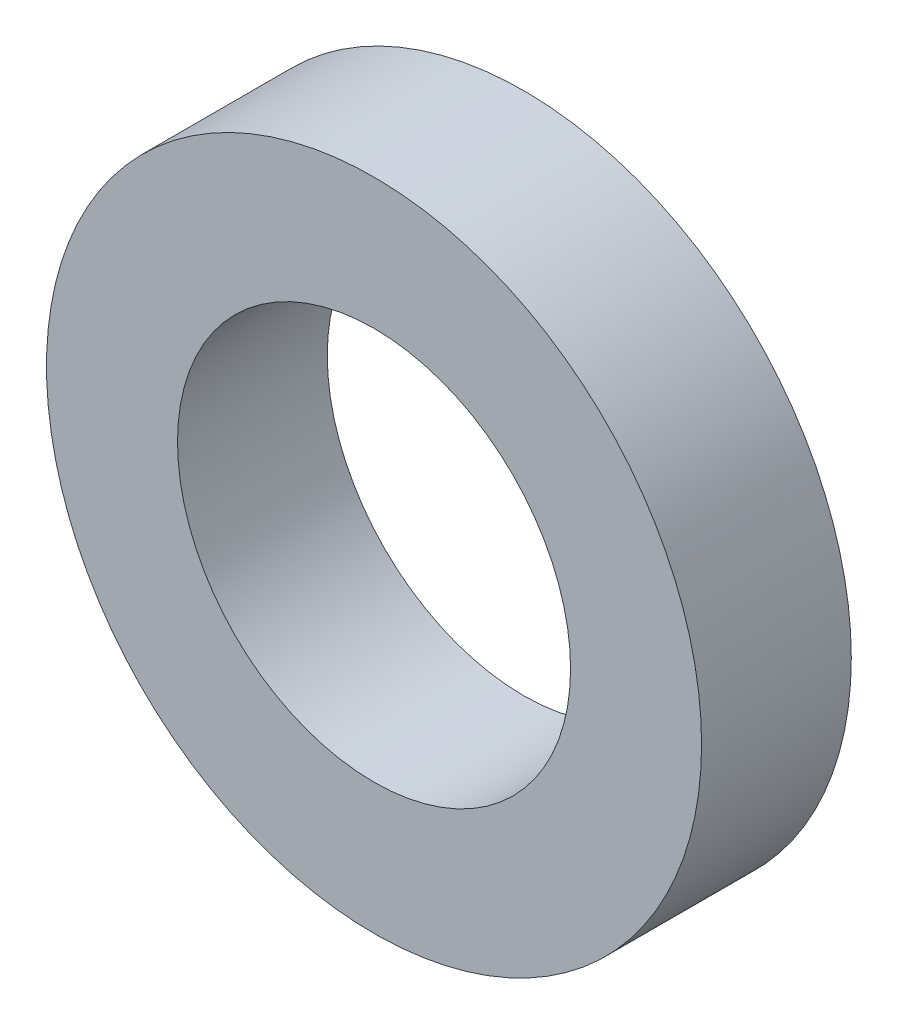
SolidWorks part; units mm, degrees
material "1.4305 (X8CrNiS18-9)"
ref_plane "Face" through (0, 0, 0) normal (0, 0, 1) x (1, 0, 0)
ref_plane "Dessus" through (0, 0, 0) normal (0, 1, 0) x (1, 0, 0)
ref_plane "Droite" through (0, 0, 0) normal (1, 0, 0) x (0, 0, -1)
sketch "Esquisse1" plane through (0, 0, 0) normal (0, 0, 1) x (1, 0, 0)
  circle A0 centre (0, 0) radius 1.75
  circle A1 centre (0, 0) radius 1.05
  dimension "D1" = 2.1
  dimension "D2" = 3.5
extrude "Boss.-Extru.1" add sketch "Esquisse1" along normal mid plane 0.8
